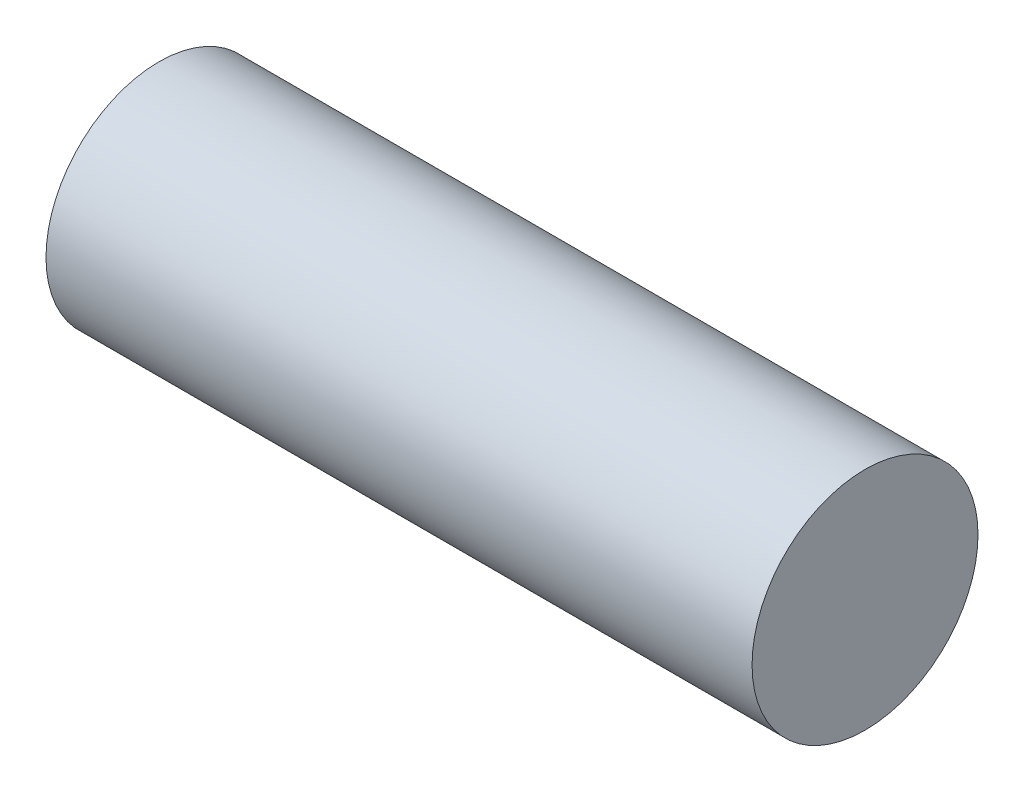
SolidWorks part; units mm, degrees
material "1.5714 (16NiCr4)"
ref_plane "Front Plane" through (0, 0, 0) normal (0, 0, 1) x (1, 0, 0)
ref_plane "Top Plane" through (0, 0, 0) normal (0, 1, 0) x (1, 0, 0)
ref_plane "Right Plane" through (0, 0, 0) normal (1, 0, 0) x (0, 0, -1)
sketch "Schizzo1" plane through (0, 0, 0) normal (1, 0, 0) x (0, 0, -1)
  circle A0 centre (0, 0) radius 4
  dimension "D1" = 8
extrude "Estrusione-Estrusione1" add sketch "Schizzo1" along normal blind 25
